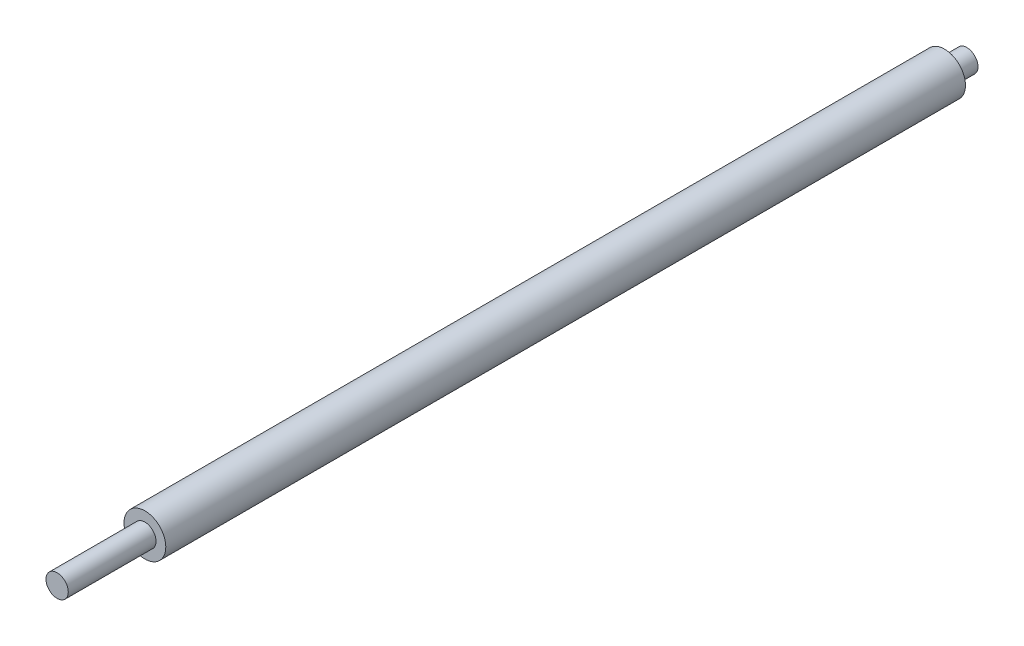
SolidWorks part; units mm, degrees
ref_plane "前视基准面" through (0, 0, 0) normal (0, 0, 1) x (1, 0, 0)
ref_plane "上视基准面" through (0, 0, 0) normal (0, 1, 0) x (1, 0, 0)
ref_plane "右视基准面" through (0, 0, 0) normal (1, 0, 0) x (0, 0, -1)
sketch "草图1" plane through (0, 0, 0) normal (0, 0, 1) x (1, 0, 0)
  circle A0 centre (0, 0) radius 4
  dimension "D1" = 8
extrude "凸台-拉伸1" add sketch "草图1" along normal blind 8
sketch "草图2" plane through (0, 0, 8) normal (0, 0, 1) x (1, 0, 0)
  circle A0 centre (0, 0) radius 7.5
  dimension "D1" = 15
extrude "凸台-拉伸2" add sketch "草图2" along normal blind 287
sketch "草图3" plane through (0, 0, 295) normal (0, 0, 1) x (1, 0, 0)
  circle A0 centre (0, 0) radius 4
  dimension "D1" = 8
extrude "凸台-拉伸3" add sketch "草图3" along normal blind 31.5
